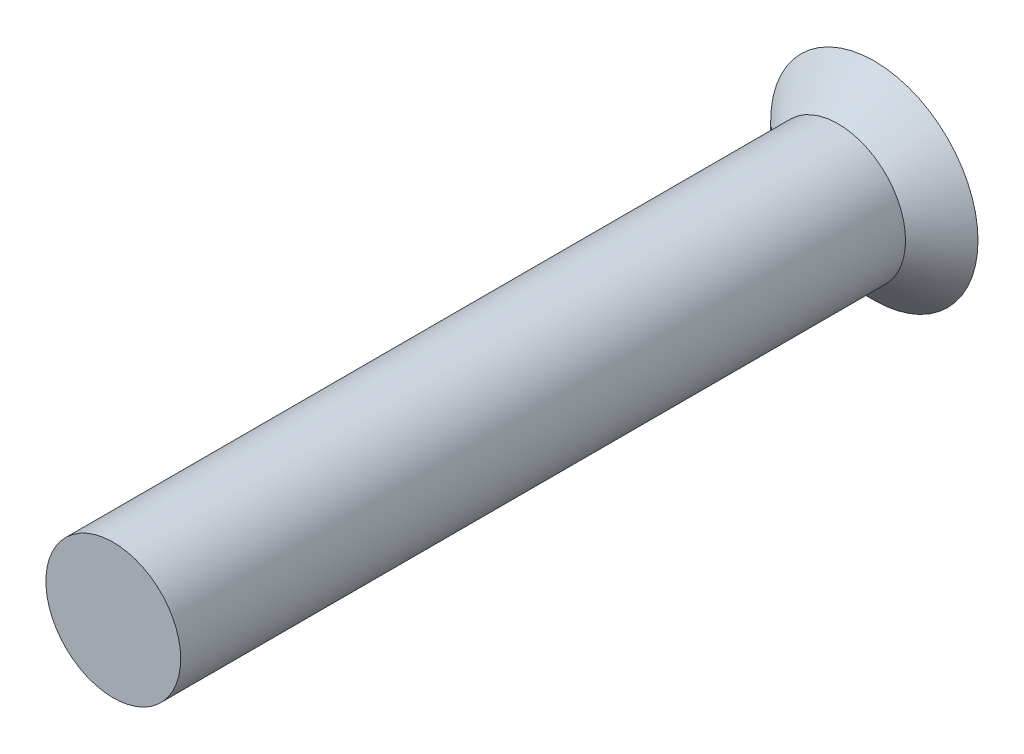
SolidWorks part; units mm, degrees
material "AISI 1020 Steel, Cold Rolled"
ref_plane "Front Plane" through (0, 0, 0) normal (0, 0, 1) x (1, 0, 0)
ref_plane "Top Plane" through (0, 0, 0) normal (0, 1, 0) x (1, 0, 0)
ref_plane "Right Plane" through (0, 0, 0) normal (1, 0, 0) x (0, 0, -1)
sketch "Sketch1" plane through (0, 0, 0) normal (0, 0, 1) x (1, 0, 0)
  circle A0 centre (0, 0) radius 0.465
  dimension "D1" = 0.93
extrude "Boss-Extrude1" add sketch "Sketch1" along normal mid plane 5 contours A0
sketch "Sketch2" plane through (0, 0, 0) normal (1, 0, 0) x (0, 0, -1)
  line L1 (2.75, 0.715) -> (2.75, 0)
  line L2 (2.75, 0) -> (2.5, 0)
  line L3 (2.5, -0.465) -> (2.5, 0.465) construction
  line L4 (2.5, 0) -> (2.5, 0.465)
  line L5 (2.5, 0.465) -> (2.75, 0.715)
  dimension "D1" = 0.25
ref_axis "Axis1" through (0, 0, 2.0805) along (0, 0, -1)
revolve "Revolve1" add sketch "Sketch2" angle 360 about axis through (0, 0, 2.0805) along (0, 0, -1)
sketch "Sketch3" plane through (0, 0, -2.75) normal (0, 0, -1) x (-1, 0, 0)
  line L0 (0.1, 0.6) -> (-0.1, 0.6)
  line L1 (-0.1, 0.6) -> (-0.1, 0.1)
  line L2 (-0.1, 0.1) -> (-0.6, 0.1)
  line L3 (-0.6, 0.1) -> (-0.6, -0.1)
  line L4 (-0.6, -0.1) -> (-0.1, -0.1)
  line L5 (-0.1, -0.1) -> (-0.1, -0.6)
  line L6 (-0.1, -0.6) -> (0.1, -0.6)
  line L7 (0.1, -0.6) -> (0.1, -0.1)
  line L8 (0.1, -0.1) -> (0.6, -0.1)
  line L9 (0.6, -0.1) -> (0.6, 0.1)
  line L10 (0.6, 0.1) -> (0.1, 0.1)
  line L11 (0.1, 0.1) -> (0.1, 0.6)
  line L12 (0, 0.7865) -> (0, -0.7865) construction
  line L13 (0.7865, 0) -> (-0.7865, 0) construction
  point P11 (0, 0.6)
  point P15 (-0.6, 0)
  dimension "D1" = 0.2
  dimension "D2" = 0.2
  dimension "D3" = 0.5
  dimension "D4" = 0.5
extrude "Cut-Extrude1" cut sketch "Sketch3" against normal blind 0.1
